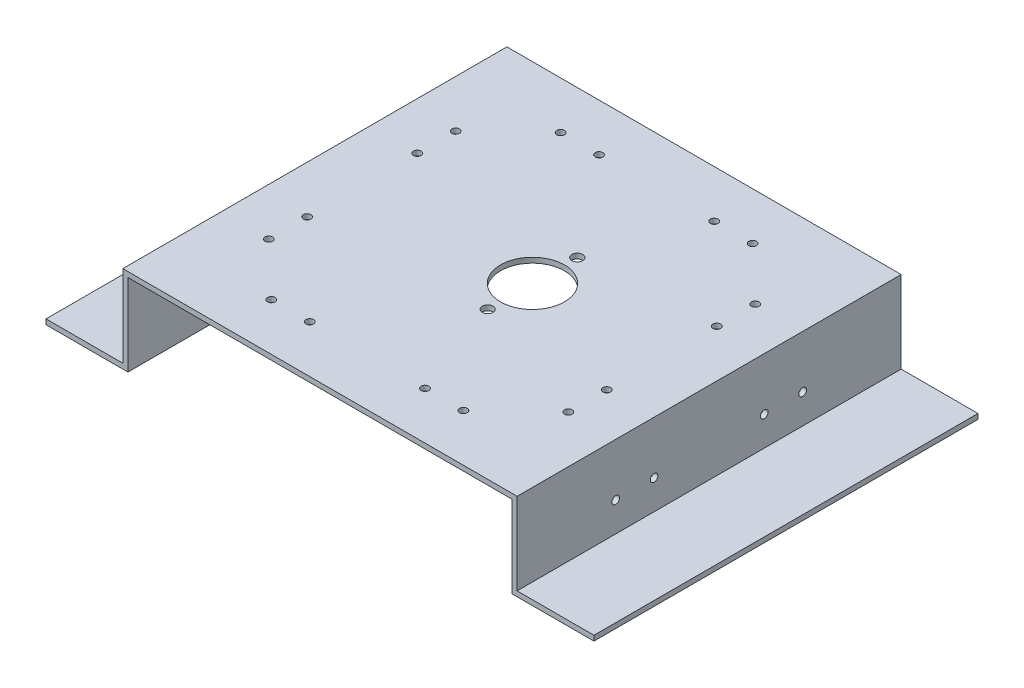
SolidWorks part; units mm, degrees
ref_plane "Front Plane" through (0, 0, 0) normal (0, 0, 1) x (1, 0, 0)
ref_plane "Top Plane" through (0, 0, 0) normal (0, 1, 0) x (1, 0, 0)
ref_plane "Right Plane" through (0, 0, 0) normal (1, 0, 0) x (0, 0, -1)
sketch "Sketch1" plane through (0, 0, 0) normal (0, 0, 1) x (1, 0, 0)
  line L0 (-77, 17) -> (77, 17)
  line L1 (77, 17) -> (77, -15)
  line L2 (77, -15) -> (107, -15)
  line L3 (107, -15) -> (107, -17)
  line L4 (107, -17) -> (75, -17)
  line L5 (75, -17) -> (75, 15)
  line L6 (75, 15) -> (-75, 15)
  line L7 (-75, 15) -> (-75, -17)
  line L8 (-75, -17) -> (-107, -17)
  line L9 (-107, -17) -> (-107, -15)
  line L10 (-107, -15) -> (-77, -15)
  line L11 (-77, -15) -> (-77, 17)
  line L12 (-82.7586, 0) -> (103.4483, 0) construction
  line L13 (0, 55.3103) -> (0, -47.8621) construction
  dimension "D1" = 154
  dimension "D2" = 2
  dimension "D3" = 2
  dimension "D4" = 2
  dimension "D5" = 2
  dimension "D6" = 2
  dimension "D7" = 32
  dimension "D8" = 32
  dimension "D9" = 17
  dimension "D10" = 77
  dimension "D11" = 30
  dimension "D12" = 30
extrude "Boss-Extrude1" add sketch "Sketch1" along normal blind 150
sketch "Sketch2" plane through (0, 17, 0) normal (0, 1, 0) x (1, 0, 0)
  line L0 (0, 50.632) -> (0, -122.4088) construction
  line L1 (-127.6985, -75) -> (156.3844, -75) construction
  circle A2 centre (8, -75) radius 12.5
  point P5 (8, -75)
  dimension "D3" = 25
  dimension "D1" = 75
  dimension "D2" = 8
extrude "Cut-Extrude1" cut sketch "Sketch2" against normal up to next
sketch "Sketch3" plane through (0, 17, 0) normal (0, 1, 0) x (1, 0, 0)
  line L0 (0, 32.7241) -> (0, -138.4166) construction
  line L1 (-101.4622, -75) -> (97.2013, -75) construction
  line L2 (77, 0) -> (-77, 0) construction
  line L3 (8, 26.6522) -> (8, -134.0169) construction
  circle A0 centre (8, -57.5) radius 2.1
  circle A1 centre (8, -92.5) radius 2.1
  point P9 (8, -57.5)
  dimension "D1" = 75
  dimension "D2" = 8
  dimension "D4" = 4.2
  dimension "D3" = 17.5
extrude "Cut-Extrude2" cut sketch "Sketch3" against normal up to next
sketch "Sketch4" plane through (0, 15, 0) normal (0, -1, 0) x (1, 0, 0)
  line L0 (0, -11.2871) -> (0, 162.4151) construction
  line L1 (-137.047, 75) -> (146.0651, 75) construction
  line L2 (-75, 0) -> (75, 0) construction
  line L4 (75, 150) -> (75, 0) construction
  line L5 (-135.047, 131.5) -> (153.3982, 131.5) construction
  line L6 (58.5, 172.2175) -> (58.5, -11.2871) construction
  line L7 (-75, 150) -> (75, 150) construction
  line L10 (-135.047, 18.5) -> (153.3982, 18.5) construction
  line L11 (-58.5, 172.2175) -> (-58.5, -11.2871) construction
  line L12 (-30, 172.2175) -> (-30, -45.7098) construction
  line L13 (-168.4927, 104) -> (180.2969, 104) construction
  line L14 (30, 172.2175) -> (30, -45.7098) construction
  line L15 (-168.4927, 46) -> (180.2969, 46) construction
  point P27 (-58.5, 111.5)
  point P28 (-58.5, 96.5)
  point P29 (-37.5, 131.5)
  point P30 (-22.5, 131.5)
  point P34 (22.5, 131.5)
  point P35 (37.5, 131.5)
  point P36 (37.5, 18.5)
  point P37 (22.5, 18.5)
  point P38 (-22.5, 18.5)
  point P39 (-37.5, 18.5)
  point P42 (-58.5, 38.5)
  point P43 (-58.5, 53.5)
  point P44 (58.5, 38.5)
  point P45 (58.5, 53.5)
  point P46 (58.5, 96.5)
  point P47 (58.5, 111.5)
  dimension "D1" = 75
  dimension "D2" = 18.5
  dimension "D4" = 30
  dimension "D6" = 15
  dimension "D7" = 15
  dimension "D3" = 16.5
  dimension "D5" = 29
hole_wizard "Ø3.0mm Dowel Hole1" positions "Sketch5" profile "Sketch6" hole size "Ø3.0" standard "ANSI Metric" end condition up to next
sketch "Sketch5" plane through (0, 15, 0) normal (0, -1, 0) x (-1, 0, 0)
  point P0 (58.5, -111.5)
  point P3 (58.5, -96.5)
  point P6 (37.5, -131.5)
  point P9 (22.5, -131.5)
  point P12 (-22.5, -131.5)
  point P15 (-37.5, -131.5)
  point P18 (-58.5, -111.5)
  point P21 (-58.5, -96.5)
  point P24 (-58.5, -53.5)
  point P27 (-58.5, -38.5)
  point P30 (-37.5, -18.5)
  point P33 (-22.5, -18.5)
  point P36 (22.5, -18.5)
  point P39 (37.5, -18.5)
  point P42 (58.5, -53.5)
  point P45 (58.5, -38.5)
sketch "Sketch6" plane through (-58.5, 15, 111.5) normal (1, 0, 0) x (0, 0, -1)
  line L0 (0, 0) -> (0, 2)
  line L1 (0, 2) -> (1.5, 2)
  line L2 (1.5, 2) -> (1.5, 0)
  line L5 (1.5, 0) -> (0, 0)
  line L11 (0, -6.35) -> (0, 107.95) construction
  dimension "Thru Hole Dia." = 3
  dimension "Thru Hole Depth" = 2
sketch "Sketch7" plane through (75, 0, 0) normal (-1, 0, 0) x (0, 0, 1)
  line L0 (-14.5676, -3.5) -> (173.2717, -3.5) construction
  line L2 (75, 30.0978) -> (75, -33.5483) construction
  line L3 (0, 15) -> (0, -17) construction
  line L4 (104, 26.9437) -> (104, -24.0401) construction
  line L5 (46, 26.9437) -> (46, -24.0401) construction
  line L6 (150, 15) -> (0, 15) construction
  point P10 (96.5, -3.5)
  point P13 (111.5, -3.5)
  point P20 (53.5, -3.5)
  point P21 (38.5, -3.5)
  dimension "D2" = 75
  dimension "D3" = 15
  dimension "D1" = 18.5
hole_wizard "Ø3.0mm Dowel Hole2" positions "Sketch8" profile "Sketch9" hole size "Ø3.0" standard "ANSI Metric" end condition up to next
sketch "Sketch8" plane through (75, 0, 0) normal (-1, 0, 0) x (0, 0, 1)
  point P0 (38.5, -3.5)
  point P3 (53.5, -3.5)
  point P6 (96.5, -3.5)
  point P9 (111.5, -3.5)
sketch "Sketch9" plane through (75, -3.5, 38.5) normal (0, 1, 0) x (0, 0, 1)
  line L0 (0, 0) -> (0, 2.001)
  line L1 (0, 2.001) -> (1.5, 2.001)
  line L2 (1.5, 2.001) -> (1.5, 0)
  line L5 (1.5, 0) -> (0, 0)
  line L11 (0, -6.35) -> (0, 107.95) construction
  dimension "Thru Hole Dia." = 3
  dimension "Thru Hole Depth" = 2.001
mirror "Mirror1" about plane through (0, 0, 0) normal (1, 0, 0) of "Ø3.0mm Dowel Hole2"
equation "\"TopLen\"= 154"
equation "\"D1@Sketch1\"=\"TopLen\""
equation "\"Thick\"=2"
equation "\"D2@Sketch1\"=\"Thick\""
equation "\"D3@Sketch1\"=\"Thick\""
equation "\"D4@Sketch1\"=\"Thick\""
equation "\"D5@Sketch1\"=\"Thick\""
equation "\"D6@Sketch1\"=\"Thick\""
equation "\"Height\"= 32"
equation "\"D7@Sketch1\"=\"Height\""
equation "\"D8@Sketch1\"=\"Height\""
equation "\"D9@Sketch1\"=(\"Height\"+\"Thick\")/2"
equation "\"D10@Sketch1\"=\"TopLen\"/2"
equation "\"D1@Boss-Extrude1\"=\"TopLen\"-4"
equation "\"BottomLen\"= 30"
equation "\"D11@Sketch1\"=\"BottomLen\""
equation "\"D12@Sketch1\"=\"BottomLen\""
equation "\"D1@Sketch2\"=(\"TopLen\"-4)/2"
equation "\"D1@Sketch3\"=(\"TopLen\"-4)/2"
equation "\"D1@Sketch4\"=(\"TopLen\"-4)/2"
equation "\"Hole-Wall_Dist\"= 16.5"
equation "\"Hole-Hole-Dist\"= 15"
equation "\"D2@Sketch4\"=\"Hole-Wall_Dist\"+2"
equation "\"D4@Sketch4\"=(\"TopLen\"-4-30)/4"
equation "\"D6@Sketch4\"=\"Hole-Hole-Dist\""
equation "\"D7@Sketch4\"=\"Hole-Hole-Dist\""
equation "\"D3@Sketch4\"=\"Hole-Wall_Dist\""
equation "\"D5@Sketch4\"=(\"TopLen\"-8-30)/4"
equation "\"D2@Sketch7\"=(\"TopLen\"-4)/2"
equation "\"D3@Sketch7\"=\"Hole-Hole-Dist\""
equation "\"D1@Sketch7\"=\"Hole-Wall_Dist\"+2"
